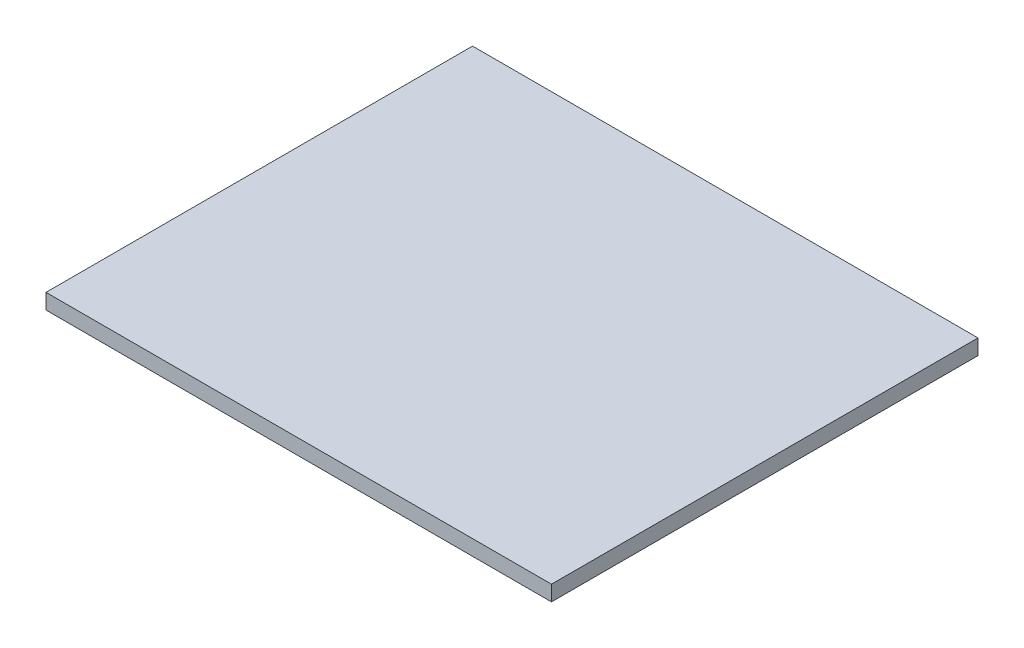
SolidWorks part; units mm, degrees
ref_plane "Front" through (0, 0, 0) normal (0, 0, 1) x (1, 0, 0)
ref_plane "Top" through (0, 0, 0) normal (0, 1, 0) x (1, 0, 0)
ref_plane "Right" through (0, 0, 0) normal (1, 0, 0) x (0, 0, -1)
sketch "Sketch1" plane through (0, 0, 0) normal (0, 1, 0) x (1, 0, 0)
  line L1 (-44.44, 37.5) -> (44.44, 37.5)
  line L2 (-44.44, 37.5) -> (-44.44, -37.5)
  line L3 (-44.44, -37.5) -> (44.44, -37.5)
  line L4 (44.44, 37.5) -> (44.44, -37.5)
  line L5 (-44.44, 37.5) -> (44.44, -37.5) construction
  line L6 (-44.44, -37.5) -> (44.44, 37.5) construction
  point P4 (0, 0)
  dimension "D1" = 75
  dimension "D2" = 88.88
extrude "Boss-Extrude1" add sketch "Sketch1" along normal blind 2.7
